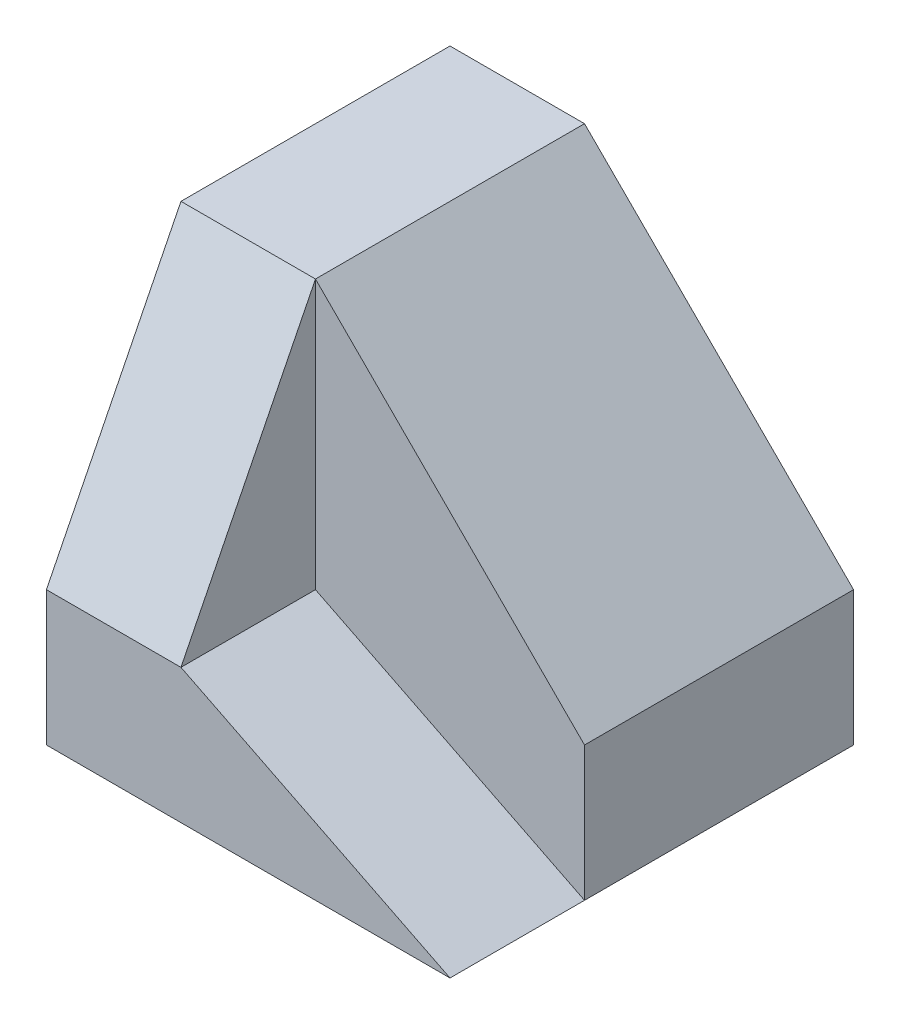
SolidWorks part; units mm, degrees
ref_plane "Alzado" through (0, 0, 0) normal (0, 0, 1) x (1, 0, 0)
ref_plane "Planta" through (0, 0, 0) normal (0, 1, 0) x (1, 0, 0)
ref_plane "Vista lateral" through (0, 0, 0) normal (1, 0, 0) x (0, 0, -1)
sketch "Croquis1" plane through (0, 0, 0) normal (0, 0, 1) x (1, 0, 0)
  line L0 (0, 0) -> (60, 0)
  line L1 (60, 0) -> (60, 20)
  line L2 (60, 20) -> (20, 60)
  line L3 (20, 60) -> (0, 60)
  line L4 (0, 60) -> (0, 0)
  dimension "D1" = 60
  dimension "D2" = 20
extrude "Saliente-Extruir1" add sketch "Croquis1" against normal blind 60
sketch "Croquis2" plane through (0, 0, 0) normal (0, 0, 1) x (1, 0, 0)
  line L0 (20, 60) -> (20, 20)
  line L1 (20, 20) -> (60, 0)
  line L2 (0, 0) -> (60, 0) construction
  line L3 (60, 0) -> (60, 20) construction
  line L4 (60, 20) -> (20, 60) construction
  line L5 (60, 0) -> (60, 20)
  line L6 (60, 20) -> (20, 60)
  dimension "D1" = 20
extrude "Cortar-Extruir1" cut sketch "Croquis2" against normal blind 20
sketch "Croquis3" plane through (20, 0, 0) normal (1, 0, 0) x (0, 0, -1)
  line L0 (0, 20) -> (20, 60)
  line L1 (20, 60) -> (0, 60)
  line L2 (0, 60) -> (0, 20)
extrude "Cortar-Extruir2" cut sketch "Croquis3" against normal up to next
